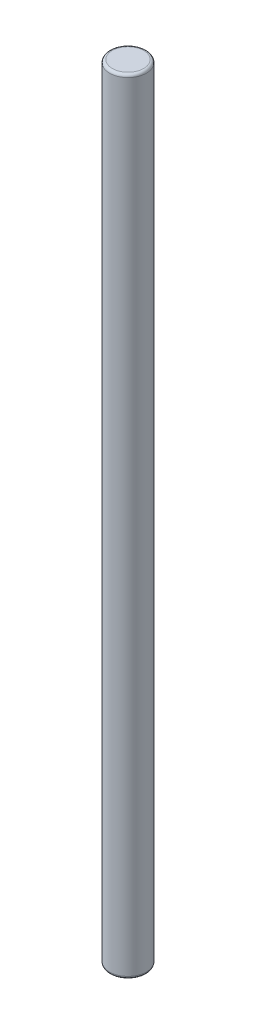
SolidWorks part; units mm, degrees
ref_plane "Front" through (0, 0, 0) normal (0, 0, 1) x (1, 0, 0)
ref_plane "Top" through (0, 0, 0) normal (0, 1, 0) x (1, 0, 0)
ref_plane "Right" through (0, 0, 0) normal (1, 0, 0) x (0, 0, -1)
sketch "Sketch1" plane through (0, 0, 0) normal (0, 1, 0) x (1, 0, 0)
  circle A0 centre (0, 0) radius 0.1715
  dimension "D1" = 0.3429
extrude "Boss-Extrude1" add sketch "Sketch1" along normal blind 7.3152
fillet "Fillet1" radius 0.0254 2 edges at (0, 0, 0.1715) (0, 7.3152, 0.1715)
